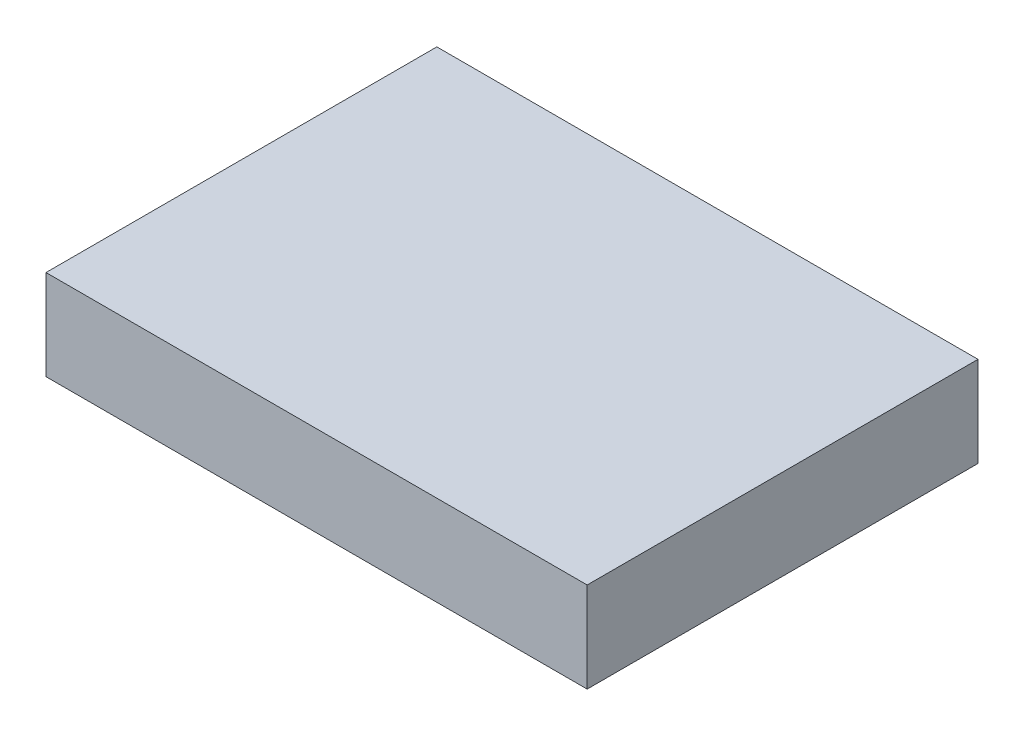
SolidWorks part; units mm, degrees
ref_plane "Front Plane" through (0, 0, 0) normal (0, 0, 1) x (1, 0, 0)
ref_plane "Top Plane" through (0, 0, 0) normal (0, 1, 0) x (1, 0, 0)
ref_plane "Right Plane" through (0, 0, 0) normal (1, 0, 0) x (0, 0, -1)
sketch "Sketch1" plane through (0, 0, 0) normal (0, 1, 0) x (1, 0, 0)
  line L1 (0, 0) -> (180, 0)
  line L2 (0, 0) -> (0, 130)
  line L3 (0, 130) -> (180, 130)
  line L4 (180, 0) -> (180, 130)
  dimension "D1" = 180
  dimension "D2" = 130
extrude "Extrude1" add sketch "Sketch1" along normal blind 30
